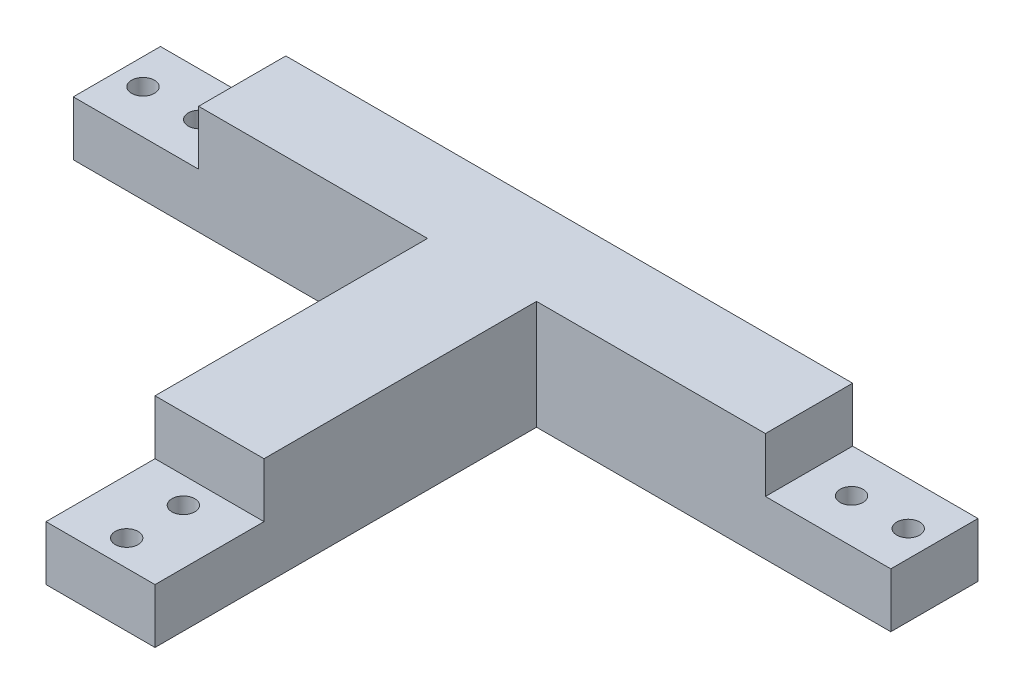
SolidWorks part; units mm, degrees
ref_plane "前视基准面" through (0, 0, 0) normal (0, 0, 1) x (1, 0, 0)
ref_plane "上视基准面" through (0, 0, 0) normal (0, 1, 0) x (1, 0, 0)
ref_plane "右视基准面" through (0, 0, 0) normal (1, 0, 0) x (0, 0, -1)
other "Configuration Table"
sketch "草图1" plane through (0, 0, 0) normal (0, 1, 0) x (1, 0, 0)
  line L1 (75, -8) -> (-75, -8)
  line L2 (75, -8) -> (75, 8)
  line L3 (75, 8) -> (-75, 8)
  line L4 (-75, -8) -> (-75, 8)
  line L5 (75, -8) -> (-75, 8) construction
  line L6 (75, 8) -> (-75, -8) construction
  point P0 (0, 0)
  dimension "D1" = 150
  dimension "D2" = 16
extrude "凸台-拉伸1" add sketch "草图1" along normal blind 10 contours L3 L4 L1 L2
sketch "草图2" plane through (0, 10, 0) normal (0, 1, 0) x (1, 0, 0)
  line L0 (75, 8) -> (-75, 8) construction
  line L1 (-55, 8) -> (55, 8)
  line L2 (-55, 8) -> (-55, -8)
  line L3 (-55, -8) -> (55, -8)
  line L4 (55, 8) -> (55, -8)
  line L5 (75, -8) -> (-75, -8) construction
  line L6 (-75, -8) -> (-75, 8) construction
  line L7 (75, -8) -> (75, 8) construction
  circle A0 centre (-70.2, 0) radius 2.1
  circle A1 centre (-59.8, 0) radius 2.1
  line M5 (75, 8) -> (-75, 8)
  line M7 (-75, -8) -> (75, -8)
  dimension "D5" = 4.2
  dimension "D8" = 4.2
  dimension "D1" = 20
  dimension "D2" = 20
  dimension "D3" = 110
  dimension "D4" = 8
  dimension "D6" = 4.8
  dimension "D7" = 4.8
extrude "凸台-拉伸2" add sketch "草图2" along normal blind 10 contours L4 L2 M5 M7 | A0
sketch "草图4" plane through (0, 10, 0) normal (0, 1, 0) x (1, 0, 0)
  line L0 (-75, -8) -> (-75, 8) construction
  line L1 (-55, 8) -> (-55, -8) construction
  line L2 (-55, -8) -> (-75, -8) construction
  circle A0 centre (-70.2, 0) radius 2.1
  circle A1 centre (-59.8, 0) radius 2.1
  dimension "D3" = 4.2
  dimension "D4" = 4.2
  dimension "D1" = 4.8
  dimension "D2" = 4.8
  dimension "D5" = 8
extrude "切除-拉伸1" cut sketch "草图4" against normal blind 10
sketch "草图5" plane through (0, 10, 0) normal (0, 1, 0) x (1, 0, 0)
  line L0 (75, -8) -> (75, 8) construction
  line L1 (55, 8) -> (55, -8) construction
  line L2 (75, -8) -> (55, -8) construction
  circle A0 centre (59.8, 0) radius 2.1
  circle A1 centre (70.2, 0) radius 2.1
  dimension "D3" = 4.2
  dimension "D4" = 4.2
  dimension "D1" = 4.8
  dimension "D2" = 4.8
  dimension "D5" = 8
extrude "切除-拉伸2" cut sketch "草图5" against normal blind 10
sketch "草图6" plane through (0, 0, 8) normal (0, 0, 1) x (1, 0, 0)
  line L0 (-55, 20) -> (55, 0) construction
  line L1 (75, 0) -> (-75, 0) construction
  line L2 (55, 20) -> (-55, 0) construction
  line L3 (-55, 20) -> (55, 20) construction
  line L4 (10, 0) -> (-10, 0)
  line L5 (10, 0) -> (10, 20)
  line L6 (10, 20) -> (-10, 20)
  line L7 (-10, 0) -> (-10, 20)
  line L8 (10, 0) -> (-10, 20) construction
  line L9 (10, 20) -> (-10, 0) construction
  point P5 (0, 10)
  dimension "D1" = 20
extrude "凸台-拉伸3" add sketch "草图6" along normal blind 50
sketch "草图7" plane through (0, 0, 58) normal (0, 0, 1) x (1, 0, 0)
  line L0 (-10, 10) -> (10, 10)
  line L1 (-10, 20) -> (-10, 0) construction
  line L2 (10, 0) -> (10, 20) construction
  line L3 (10, 10) -> (10, 0)
  line L4 (10, 0) -> (-10, 0)
  line L5 (-10, 0) -> (-10, 10)
extrude "凸台-拉伸4" add sketch "草图7" along normal blind 20
sketch "草图8" plane through (0, 10, 0) normal (0, 1, 0) x (1, 0, 0)
  line L0 (10, -78) -> (-10, -78) construction
  line L1 (10, -58) -> (-10, -58) construction
  line L2 (10, -78) -> (10, -58) construction
  circle A0 centre (0, -62.8) radius 2.1
  circle A1 centre (0, -73.2) radius 2.1
  dimension "D3" = 4.2
  dimension "D4" = 4.2
  dimension "D1" = 4.8
  dimension "D2" = 4.8
  dimension "D5" = 10
extrude "切除-拉伸3" cut sketch "草图8" against normal blind 10
sketch "草图9" plane through (0, 20, 0) normal (0, 1, 0) x (1, 0, 0)
  line L0 (-55, -8) -> (-10, -8) construction
  line L1 (-55, 8) -> (-52, 8)
  line L2 (-55, 8) -> (-55, -8)
  line L3 (-55, -8) -> (-52, -8)
  line L4 (-52, 8) -> (-52, -8)
  line L5 (10, -8) -> (55, -8) construction
  line L6 (55, 8) -> (52, 8)
  line L7 (55, 8) -> (55, -8)
  line L8 (55, -8) -> (52, -8)
  line L9 (52, 8) -> (52, -8)
  dimension "D1" = 3
  dimension "D2" = 3
extrude "切除-拉伸4" cut sketch "草图9" against normal blind 10
